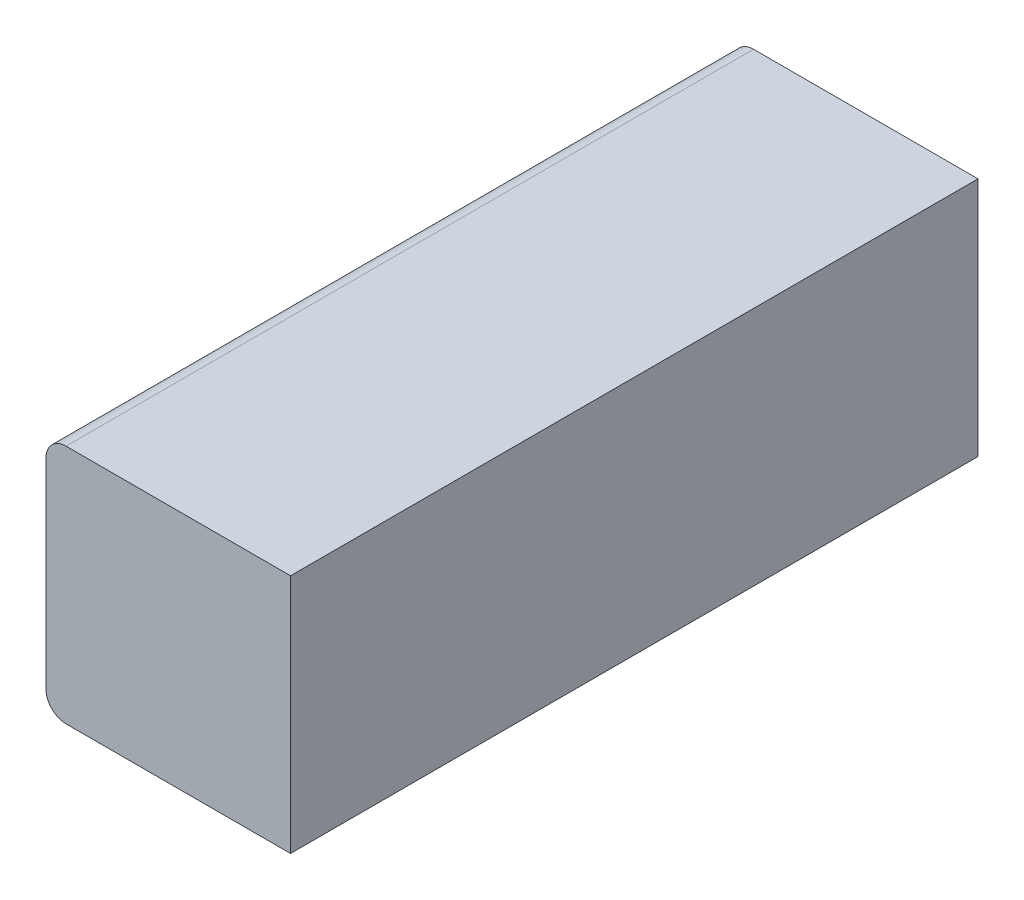
SolidWorks part; units mm, degrees
ref_plane "Plano frontal" through (0, 0, 0) normal (0, 0, 1) x (1, 0, 0)
ref_plane "Plano superior" through (0, 0, 0) normal (0, 1, 0) x (1, 0, 0)
ref_plane "Plano direito" through (0, 0, 0) normal (1, 0, 0) x (0, 0, -1)
sketch "Esboço1" plane through (0, 0, 0) normal (0, 0, 1) x (1, 0, 0)
  line L1 (0, 0) -> (610, 0)
  line L2 (0, 0) -> (0, 600)
  line L3 (0, 600) -> (610, 600)
  line L4 (610, 0) -> (610, 600)
  dimension "D1" = 610
  dimension "D2" = 600
extrude "Ressalto-extrusão1" add sketch "Esboço1" along normal blind 1715
fillet "Filete1" radius 50 2 edges at (0, 600, 857.5) (0, 0, 857.5)
